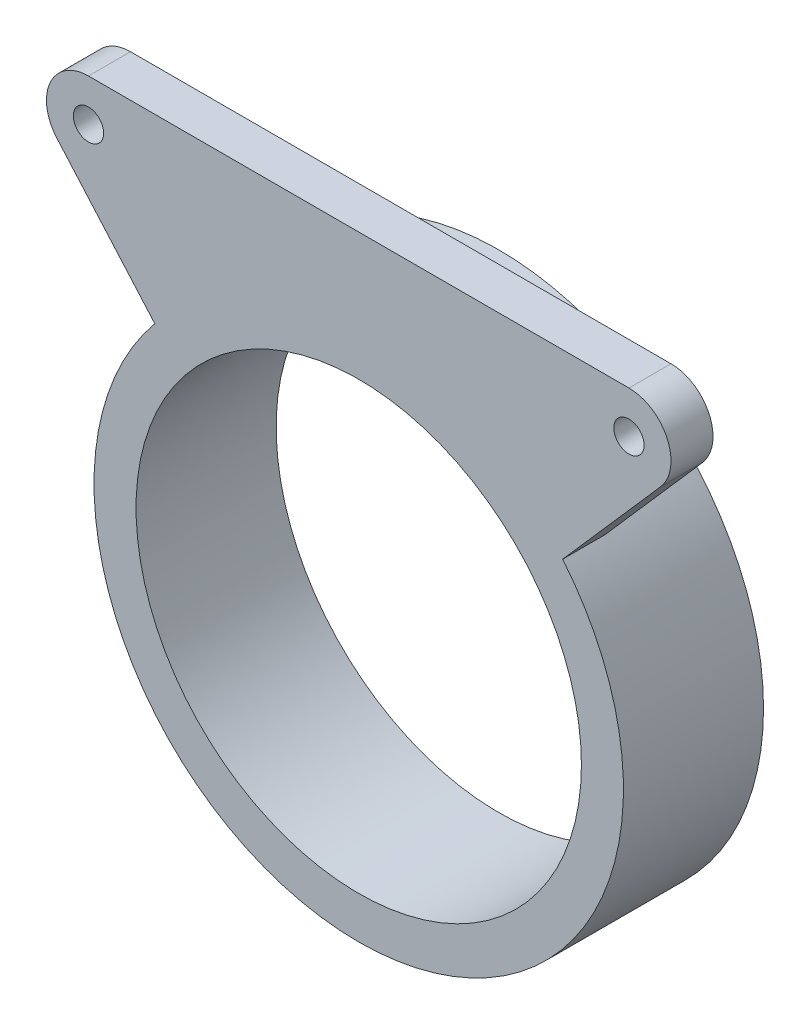
SolidWorks part; units mm, degrees
ref_plane "Front" through (0, 0, 0) normal (0, 0, 1) x (1, 0, 0)
ref_plane "Top" through (0, 0, 0) normal (0, 1, 0) x (1, 0, 0)
ref_plane "Right" through (0, 0, 0) normal (1, 0, 0) x (0, 0, -1)
sketch "Sketch1" plane through (0, 0, 0) normal (0, 0, 1) x (1, 0, 0)
  circle A0 centre (0, 0) radius 19.939 construction
  circle A1 centre (0, 0) radius 20.189
  circle A2 centre (0, 0) radius 23.999
  dimension "D1" = 39.878
  dimension "D2" = 0.25
  dimension "D3" = 3.81
extrude "Boss-Extrude1" add sketch "Sketch1" along normal blind 12.7
sketch "Sketch2" plane through (0, 0, 12.7) normal (0, 0, 1) x (1, 0, 0)
  line L0 (0, 0) -> (24.4997, 27.94) construction
  line L1 (24.4997, 27.94) -> (-24.4997, 27.94) construction
  line L2 (-24.4997, 27.94) -> (0, 0) construction
  line L3 (18.4865, 15.3036) -> (27.3644, 25.4281)
  line L4 (24.4997, 31.75) -> (-24.4997, 31.75)
  line L5 (-27.3644, 25.4281) -> (-18.4865, 15.3036)
  line L6 (0, -5.7789) -> (32.9079, 31.75) construction
  line L7 (32.9079, 31.75) -> (-32.9079, 31.75) construction
  line L8 (-32.9079, 31.75) -> (0, -5.7789) construction
  line L9 (0, 31.75) -> (0, 0) construction
  arc A0 (27.3644, 25.4281) -> (24.4997, 31.75) centre (24.4997, 27.94) ccw
  arc A1 (-24.4997, 31.75) -> (-27.3644, 25.4281) centre (-24.4997, 27.94) ccw
  circle A2 centre (-24.4997, 27.94) radius 1.375
  circle A3 centre (24.4997, 27.94) radius 1.375
  circle A5 centre (0, 0) radius 23.999 construction
  arc A6 (-18.4865, 15.3036) -> (18.4865, 15.3036) centre (0, 0) cw
  dimension "D2" = 3.81
  dimension "D4" = 48.9994
  dimension "D3" = 31.75
  dimension "D1" = 3.81
extrude "Boss-Extrude2" add sketch "Sketch2" against normal blind 3.81
sketch "Sketch3" plane through (0, 0, 8.89) normal (0, 0, -1) x (-1, 0, 0)
  circle A0 centre (-24.4997, 27.94) radius 3.81
  circle A1 centre (24.4997, 27.94) radius 3.81
  circle A2 centre (-24.4997, 27.94) radius 1.375
  circle A3 centre (24.4997, 27.94) radius 3.81
  circle M1 centre (-24.4997, 27.94) radius 1.375
  circle M2 centre (24.4997, 27.94) radius 1.375
  arc M3 (-24.4997, 31.75) -> (-27.3644, 25.4281) centre (-24.4997, 27.94) ccw
  arc M7 (27.3644, 25.4281) -> (24.4997, 31.75) centre (24.4997, 27.94) ccw
extrude "Boss-Extrude3" [suppressed] add sketch "Sketch3" along normal blind 15.24 contours A1 M7 M2 | A0 M3 M1
